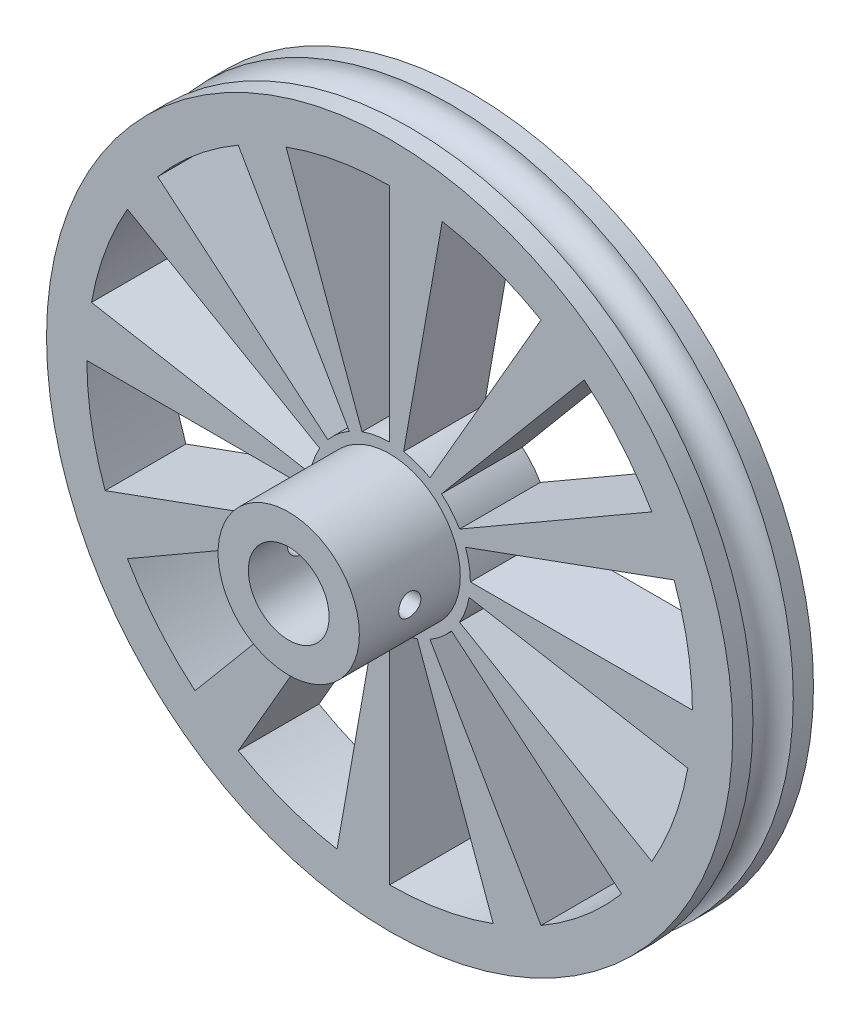
SolidWorks part; units mm, degrees
ref_plane "前视基准面" through (0, 0, 0) normal (0, 0, 1) x (1, 0, 0)
ref_plane "上视基准面" through (0, 0, 0) normal (0, 1, 0) x (1, 0, 0)
ref_plane "右视基准面" through (0, 0, 0) normal (1, 0, 0) x (0, 0, -1)
sketch "草图2" plane through (0, 0, 0) normal (0, 1, 0) x (1, 0, 0)
  line L0 (0, 0) -> (0, 27.2432) construction
  line L1 (-4, -4) -> (-4, 4)
  line L2 (-4, 4) -> (-34, 4)
  line L3 (0, 0) -> (-34, 0) construction
  line L4 (-34, 4) -> (-34, 2)
  line L5 (-7, -4) -> (-34, -4)
  line L6 (-34, -4) -> (-34, -2)
  line L7 (-4, -4) -> (-4, -14)
  line L8 (-4, -14) -> (-7, -14)
  line L9 (-7, -14) -> (-7, -4)
  arc A0 (-34, -2) -> (-34, 2) centre (-34, 0) ccw
  dimension "D1" = 30
  dimension "D2" = 2
  dimension "D3" = 8
  dimension "D4" = 4
  dimension "D5" = 3
  dimension "D6" = 10
revolve "旋转1" add sketch "草图2" angle 360 about L0
sketch "草图3" plane through (0, 0, 4) normal (0, 0, 1) x (1, 0, 0)
  line L0 (-30, 0) -> (-8, 0)
  line L1 (-29.5442, 5.2094) -> (-7.8785, 1.3892)
  line L2 (-28.1908, 10.2606) -> (-7.5175, 2.7362)
  line L3 (-25.9808, 15) -> (-6.9282, 4)
  line L4 (-22.9813, 19.2836) -> (-6.1284, 5.1423)
  line L5 (-19.2836, 22.9813) -> (-5.1423, 6.1284)
  line L6 (-15, 25.9808) -> (-4, 6.9282)
  line L7 (-10.2606, 28.1908) -> (-2.7362, 7.5175)
  line L8 (-5.2094, 29.5442) -> (-1.3892, 7.8785)
  line L9 (0, 30) -> (0, 8)
  line L10 (5.2094, 29.5442) -> (1.3892, 7.8785)
  line L11 (10.2606, 28.1908) -> (2.7362, 7.5175)
  line L12 (15, 25.9808) -> (4, 6.9282)
  line L13 (19.2836, 22.9813) -> (5.1423, 6.1284)
  line L14 (22.9813, 19.2836) -> (6.1284, 5.1423)
  line L15 (25.9808, 15) -> (6.9282, 4)
  line L16 (28.1908, 10.2606) -> (7.5175, 2.7362)
  line L17 (29.5442, 5.2094) -> (7.8785, 1.3892)
  line L18 (30, 0) -> (8, 0)
  line L19 (29.5442, -5.2094) -> (7.8785, -1.3892)
  line L20 (28.1908, -10.2606) -> (7.5175, -2.7362)
  line L21 (25.9808, -15) -> (6.9282, -4)
  line L22 (22.9813, -19.2836) -> (6.1284, -5.1423)
  line L23 (19.2836, -22.9813) -> (5.1423, -6.1284)
  line L24 (15, -25.9808) -> (4, -6.9282)
  line L25 (10.2606, -28.1908) -> (2.7362, -7.5175)
  line L26 (5.2094, -29.5442) -> (1.3892, -7.8785)
  line L27 (0, -30) -> (0, -8)
  line L28 (-5.2094, -29.5442) -> (-1.3892, -7.8785)
  line L29 (-10.2606, -28.1908) -> (-2.7362, -7.5175)
  line L30 (-15, -25.9808) -> (-4, -6.9282)
  line L31 (-19.2836, -22.9813) -> (-5.1423, -6.1284)
  line L32 (-22.9813, -19.2836) -> (-6.1284, -5.1423)
  line L33 (-25.9808, -15) -> (-6.9282, -4)
  line L34 (-28.1908, -10.2606) -> (-7.5175, -2.7362)
  line L35 (-29.5442, -5.2094) -> (-7.8785, -1.3892)
  arc A0 (-8, 0) -> (-7.5175, -2.7362) centre (0, 0) ccw
  arc A1 (-30, 0) -> (-28.1908, -10.2606) centre (0, 0) ccw
  arc A2 (0, 30) -> (-10.2606, 28.1908) centre (0, 0) ccw
  arc A3 (0, 8) -> (-2.7362, 7.5175) centre (0, 0) ccw
  arc A4 (30, 0) -> (28.1908, 10.2606) centre (0, 0) ccw
  arc A5 (8, 0) -> (7.5175, 2.7362) centre (0, 0) ccw
  arc A6 (0, -8) -> (2.7362, -7.5175) centre (0, 0) ccw
  arc A7 (0, -30) -> (10.2606, -28.1908) centre (0, 0) ccw
  arc A8 (25.9808, -15) -> (29.5442, -5.2094) centre (0, 0) ccw
  arc A9 (6.9282, -4) -> (7.8785, -1.3892) centre (0, 0) ccw
  arc A10 (15, -25.9808) -> (22.9813, -19.2836) centre (0, 0) ccw
  arc A11 (4, -6.9282) -> (6.1284, -5.1423) centre (0, 0) ccw
  arc A12 (25.9808, 15) -> (19.2836, 22.9813) centre (0, 0) ccw
  arc A13 (6.9282, 4) -> (5.1423, 6.1284) centre (0, 0) ccw
  arc A14 (4, 6.9282) -> (1.3892, 7.8785) centre (0, 0) ccw
  arc A15 (15, 25.9808) -> (5.2094, 29.5442) centre (0, 0) ccw
  arc A16 (-4, 6.9282) -> (-6.1284, 5.1423) centre (0, 0) ccw
  arc A17 (-15, 25.9808) -> (-22.9813, 19.2836) centre (0, 0) ccw
  arc A18 (-6.9282, 4) -> (-7.8785, 1.3892) centre (0, 0) ccw
  arc A19 (-25.9808, 15) -> (-29.5442, 5.2094) centre (0, 0) ccw
  arc A20 (-25.9808, -15) -> (-19.2836, -22.9813) centre (0, 0) ccw
  arc A21 (-6.9282, -4) -> (-5.1423, -6.1284) centre (0, 0) ccw
  arc A22 (-15, -25.9808) -> (-5.2094, -29.5442) centre (0, 0) ccw
  arc A23 (-4, -6.9282) -> (-1.3892, -7.8785) centre (0, 0) ccw
  dimension "D2" = 30
  dimension "D3" = 8
  dimension "D1" = 36
extrude "切除-拉伸1" cut sketch "草图3" against normal up to next contours A19 L1 A18 L3 | A17 L4 A16 L6 | A2 L7 A3 L9 | A15 L10 A14 L12 | A12 L13 A13 L15 | A4 L16 A5 L18 | A8 L19 A9 L21 | A10 L22 A11 L24 | A7 L25 A6 L27 | A22 L28 A23 L30 | A20 L31 A21 L33 | A1 L34 A0 L0
sketch "草图4" plane through (0, 0, 0) normal (1, 0, 0) x (0, 0, -1)
  line L0 (0, 0) -> (-21.4762, 0) construction
  line L1 (-14, 7) -> (-14, -7) construction
  circle A0 centre (-9, 0) radius 1.1
  dimension "D1" = 2.2
  dimension "D2" = 5
extrude "切除-拉伸2" cut sketch "草图4" against normal up to next and the other way up to next
